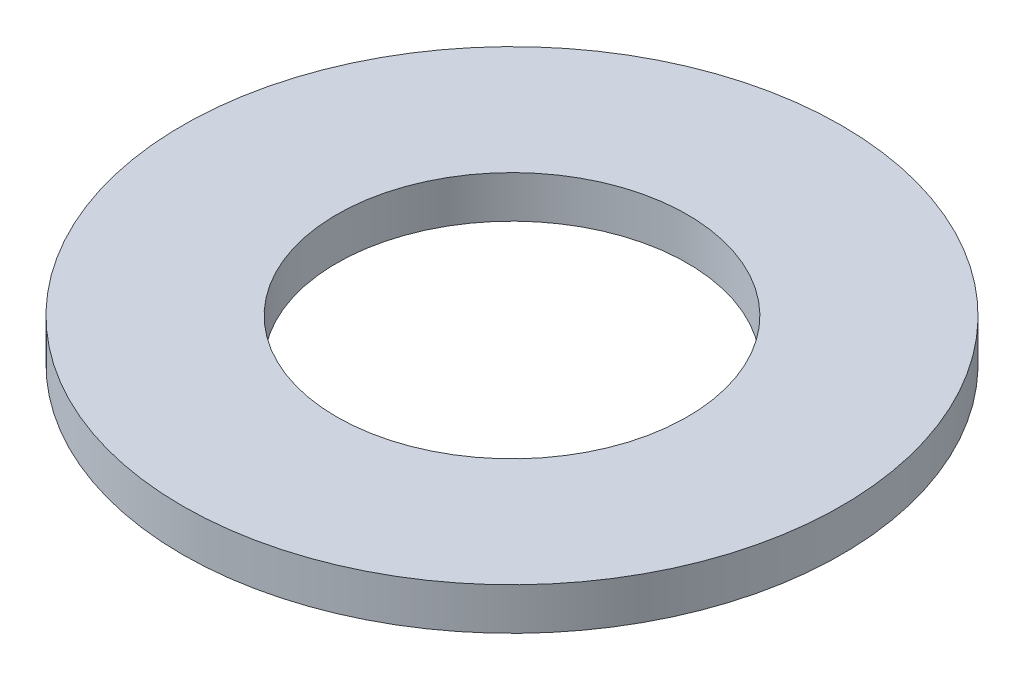
SolidWorks part; units mm, degrees
ref_plane "Front Plane" through (0, 0, 0) normal (0, 0, 1) x (1, 0, 0)
ref_plane "Top Plane" through (0, 0, 0) normal (0, 1, 0) x (1, 0, 0)
ref_plane "Right Plane" through (0, 0, 0) normal (1, 0, 0) x (0, 0, -1)
sketch "Sketch1" plane through (0, 0, 0) normal (0, 1, 0) x (1, 0, 0)
  circle A0 centre (0, 0) radius 5.969
  circle A1 centre (0, 0) radius 3.175
  dimension "D1" = 11.938
  dimension "D2" = 6.35
extrude "Boss-Extrude1" add sketch "Sketch1" along normal blind 0.762
